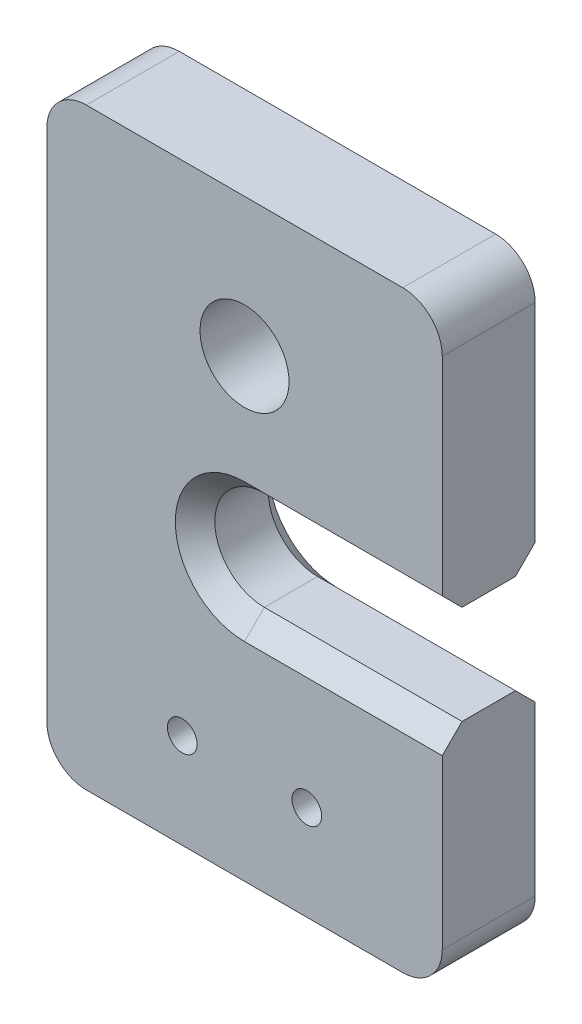
SolidWorks part; units mm, degrees
ref_plane "Front Plane" through (0, 0, 0) normal (0, 0, 1) x (1, 0, 0)
ref_plane "Top Plane" through (0, 0, 0) normal (0, 1, 0) x (1, 0, 0)
ref_plane "Right Plane" through (0, 0, 0) normal (1, 0, 0) x (0, 0, -1)
sketch "Sketch1" plane through (0, 0, 0) normal (0, 0, 1) x (1, 0, 0)
  line L0 (0, 23) -> (20, 23) construction
  line L1 (2, 0) -> (18, 0)
  line L2 (0, 2) -> (0, 28)
  line L3 (2, 30) -> (18, 30)
  line L4 (20, 2) -> (20, 28)
  line L5 (0, 4.8) -> (20, 4.8) construction
  arc A0 (18, 0) -> (20, 2) centre (18, 2) ccw
  arc A1 (20, 28) -> (18, 30) centre (18, 28) ccw
  arc A2 (2, 30) -> (0, 28) centre (2, 28) ccw
  arc A3 (0, 2) -> (2, 0) centre (2, 2) ccw
  circle A4 centre (10, 23) radius 2.25
  circle A5 centre (6.85, 4.8) radius 0.75
  circle A6 centre (13.15, 4.8) radius 0.75
  point P7 (20, 0)
  point P10 (20, 30)
  point P15 (0, 0)
  dimension "D3" = 2
  dimension "D5" = 4.5
  dimension "D7" = 1.5
  dimension "D1" = 20
  dimension "D2" = 30
  dimension "D4" = 7
  dimension "D6" = 4.8
  dimension "D8" = 6.3
  dimension "D9" = 3.15
extrude "Boss-Extrude1" add sketch "Sketch1" along normal blind 4.7
sketch "Sketch2" plane through (0, 0, 4.7) normal (0, 0, 1) x (1, 0, 0)
  line L0 (20, 16.5) -> (10, 16.5)
  line L1 (18, 30) -> (2, 30) construction
  line L3 (0, 14) -> (20, 14) construction
  line L4 (0, 28) -> (0, 2) construction
  line L5 (20, 2) -> (20, 28) construction
  line L6 (20, 11.5) -> (10, 11.5)
  line L7 (20, 16.5) -> (20, 11.5)
  circle A0 centre (10, 14) radius 2.5 construction
  arc A1 (10, 16.5) -> (10, 11.5) centre (10, 14) ccw
  dimension "D2" = 5
  dimension "D1" = 16
extrude "Cut-Extrude1" cut sketch "Sketch2" against normal through all
chamfer "Chamfer1" distance 1 angle 45 6 edges at (15, 16.5, 0) (7.5, 14, 0) (15, 11.5, 0) (15, 11.5, 4.7) (7.5, 14, 4.7) (15, 16.5, 4.7)
